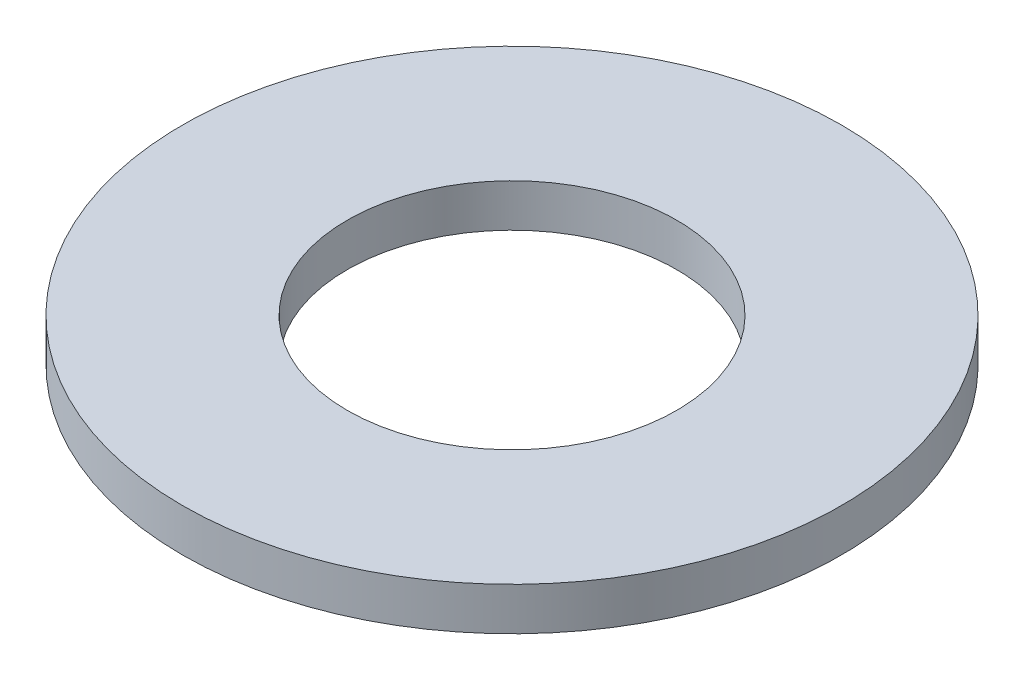
SolidWorks part; units mm, degrees
ref_plane "Front Plane" through (0, 0, 0) normal (0, 0, 1) x (1, 0, 0)
ref_plane "Top Plane" through (0, 0, 0) normal (0, 1, 0) x (1, 0, 0)
ref_plane "Right Plane" through (0, 0, 0) normal (1, 0, 0) x (0, 0, -1)
sketch "Sketch1" plane through (0, 0, 0) normal (0, 1, 0) x (1, 0, 0)
  circle A0 centre (0, 0) radius 6.35
  circle A1 centre (0, 0) radius 12.7
  dimension "D1" = 12.7
  dimension "D2" = 25.4
extrude "Boss-Extrude1" add sketch "Sketch1" along normal blind 1.651
